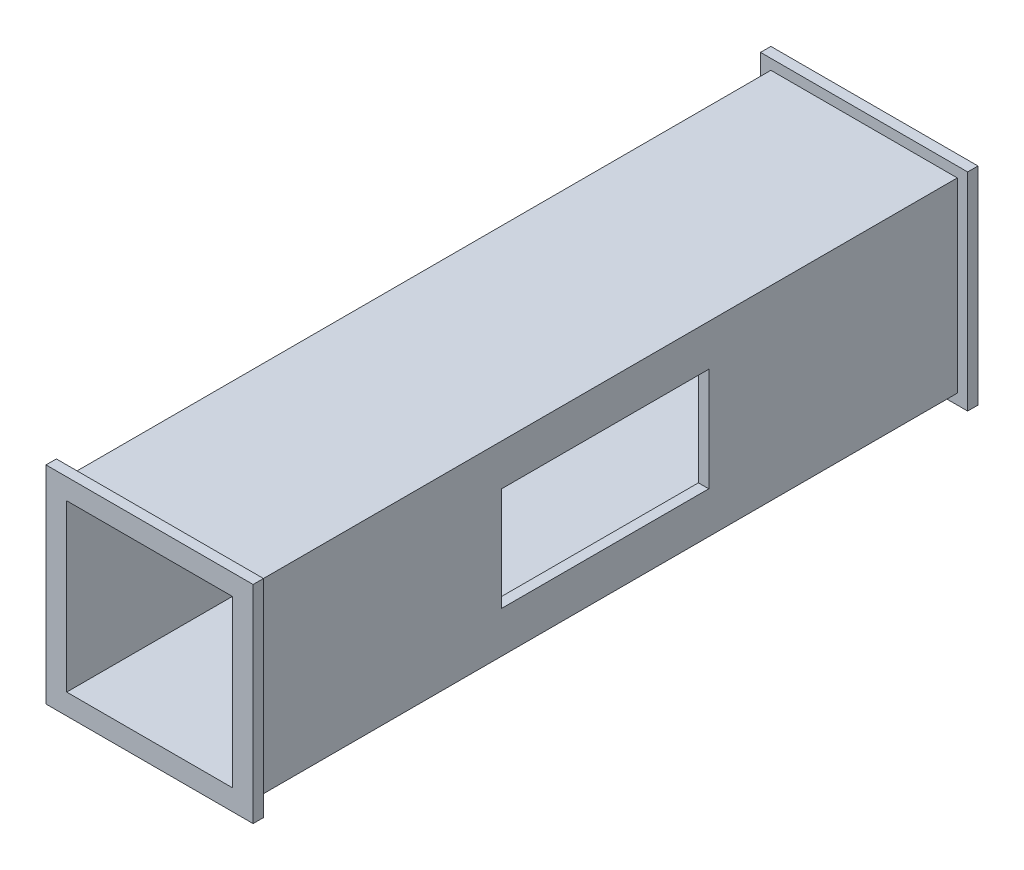
SolidWorks part; units mm, degrees
ref_plane "Front Plane" through (0, 0, 0) normal (0, 0, 1) x (1, 0, 0)
ref_plane "Top Plane" through (0, 0, 0) normal (0, 1, 0) x (1, 0, 0)
ref_plane "Right Plane" through (0, 0, 0) normal (1, 0, 0) x (0, 0, -1)
sketch "Sketch3" plane through (0, 0, 0) normal (0, 0, 1) x (1, 0, 0)
  line L1 (-45, -45) -> (45, -45)
  line L2 (-45, -45) -> (-45, 45)
  line L3 (-45, 45) -> (45, 45)
  line L4 (45, -45) -> (45, 45)
  line L5 (-45, -45) -> (45, 45) construction
  line L6 (-45, 45) -> (45, -45) construction
  point P0 (0, 0)
  dimension "D1" = 90
  dimension "D2" = 90
extrude "Boss-Extrude1" add sketch "Sketch3" along normal blind 350
shell "Shell1" thickness 5
sketch "Sketch4" plane through (45, 0, 0) normal (1, 0, 0) x (0, 0, -1)
  line L1 (-225, 25) -> (-125, 25)
  line L2 (-225, 25) -> (-225, -25)
  line L3 (-225, -25) -> (-125, -25)
  line L4 (-125, 25) -> (-125, -25)
  line L5 (-225, 25) -> (-125, -25) construction
  line L6 (-225, -25) -> (-125, 25) construction
  point P0 (-175, 0)
  point P5 (0, 0)
  dimension "D1" = 100
  dimension "D2" = 50
extrude "Cut-Extrude1" cut sketch "Sketch4" against normal blind 20
sketch "Sketch5" plane through (0, 0, 350) normal (0, 0, 1) x (1, 0, 0)
  line L4 (50, -50) -> (50, 50)
  line L5 (50, 50) -> (-50, 50)
  line L6 (-50, 50) -> (-50, -50)
  line L7 (-50, -50) -> (50, -50)
  line L8 (45, -45) -> (45, 45)
  line L9 (45, 45) -> (-45, 45)
  line L10 (-45, 45) -> (-45, -45)
  line L11 (-45, -45) -> (45, -45)
  line L12 (45, -45) -> (45, 45)
  line L13 (45, 45) -> (-45, 45)
  line L14 (-45, 45) -> (-45, -45)
  line L15 (-45, -45) -> (45, -45)
  dimension "D1" = 0
  dimension "D2" = 5
extrude "Boss-Extrude2" add sketch "Sketch5" against normal blind 5
sketch "Sketch6" plane through (0, 0, 0) normal (0, 0, -1) x (-1, 0, 0)
  line L0 (-50, 50) -> (-50, -50)
  line L1 (-50, -50) -> (50, -50)
  line L2 (50, -50) -> (50, 50)
  line L3 (50, 50) -> (-50, 50)
  line L4 (-45, 45) -> (-45, -45)
  line L5 (-45, -45) -> (45, -45)
  line L6 (45, -45) -> (45, 45)
  line L7 (45, 45) -> (-45, 45)
  line L8 (-45, 45) -> (-45, -45)
  line L9 (-45, -45) -> (45, -45)
  line L10 (45, -45) -> (45, 45)
  line L11 (45, 45) -> (-45, 45)
  dimension "D1" = 0
  dimension "D2" = 5
extrude "Boss-Extrude3" add sketch "Sketch6" against normal blind 5
